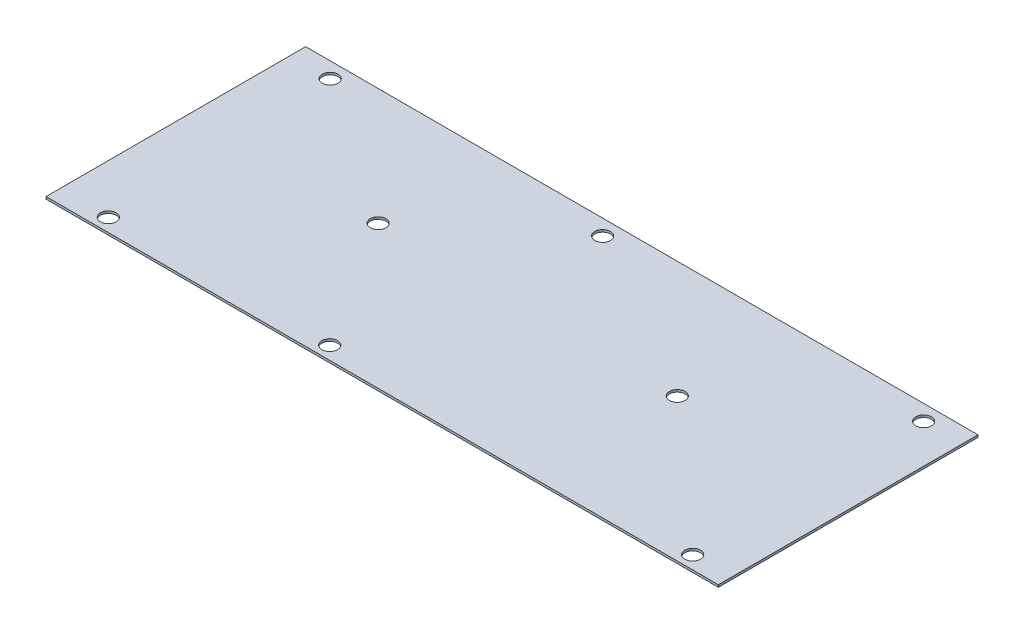
SolidWorks part; units mm, degrees
ref_plane "Alzado" through (0, 0, 0) normal (0, 0, 1) x (1, 0, 0)
ref_plane "Planta" through (0, 0, 0) normal (0, 1, 0) x (1, 0, 0)
ref_plane "Vista lateral" through (0, 0, 0) normal (1, 0, 0) x (0, 0, -1)
sketch "Croquis1" plane through (0, 0, 0) normal (0, 1, 0) x (1, 0, 0)
  line L1 (-150.0251, -57.9374) -> (150.0251, -57.9374)
  line L2 (-150.0251, -57.9374) -> (-150.0251, 57.9374)
  line L3 (-150.0251, 57.9374) -> (150.0251, 57.9374)
  line L4 (150.0251, -57.9374) -> (150.0251, 57.9374)
  circle A0 centre (-128.1049, -52.0446) radius 3.5052
  circle A1 centre (-132.1689, 51.0286) radius 3.5052
  circle A2 centre (-10.5791, 51.0286) radius 3.5052
  circle A3 centre (132.6769, 51.0286) radius 3.5052
  circle A4 centre (132.6769, -52.0446) radius 3.5052
  circle A5 centre (-29.2989, -52.0446) radius 3.5052
  circle A6 centre (67.9069, 5.8674) radius 3.5052
  circle A7 centre (-65.6209, 5.8674) radius 3.5052
  point P0 (0, 0)
  point P6 (0, 57.9374)
  point P7 (-150.0251, 0)
  dimension "D3" = 7.0104
  dimension "D1" = 115.8748
  dimension "D2" = 300.0502
  dimension "D4" = 21.9202
  dimension "D5" = 5.8928
  dimension "D6" = 63.8048
  dimension "D7" = 17.8562
  dimension "D8" = 6.9088
  dimension "D9" = 84.4042
  dimension "D10" = 120.7262
  dimension "D11" = 160.6042
  dimension "D12" = 17.3482
  dimension "D13" = 82.1182
extrude "Saliente-Extruir1" add sketch "Croquis1" along normal blind 1.016
